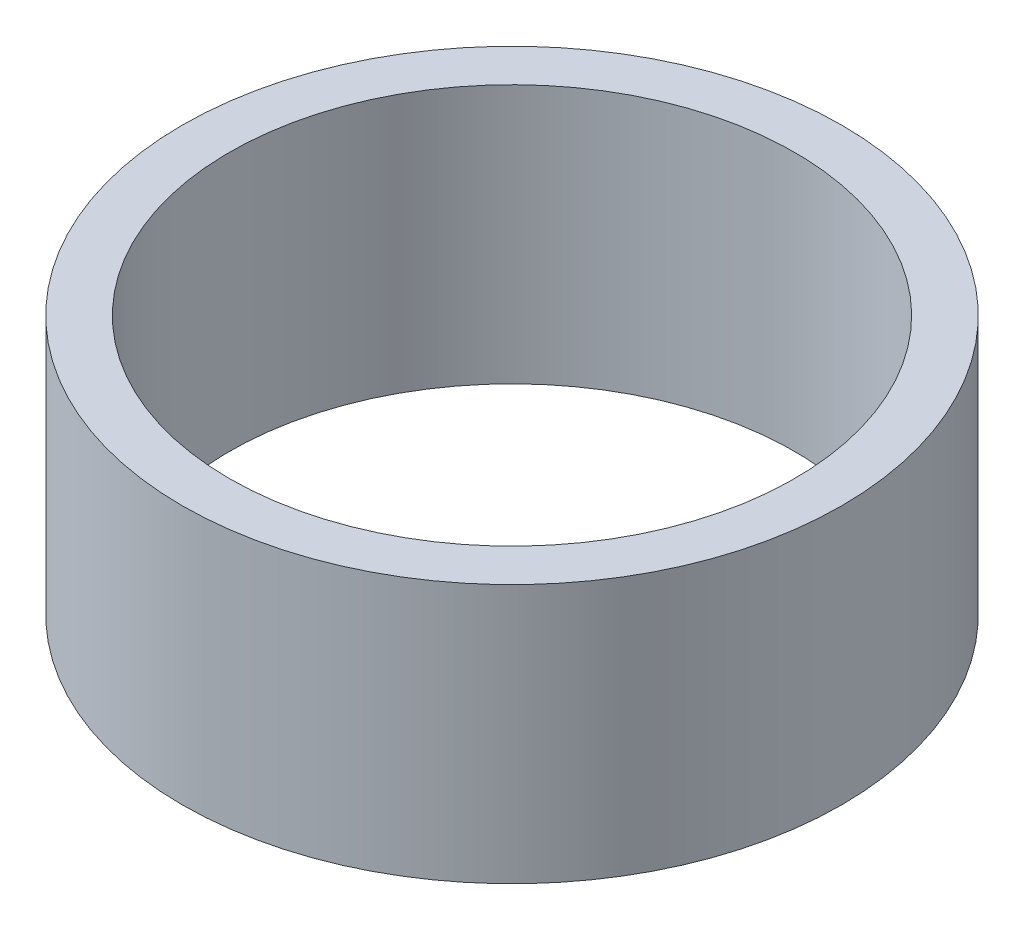
SolidWorks part; units mm, degrees
ref_plane "Front Plane" through (0, 0, 0) normal (0, 0, 1) x (1, 0, 0)
ref_plane "Top Plane" through (0, 0, 0) normal (0, 1, 0) x (1, 0, 0)
ref_plane "Right Plane" through (0, 0, 0) normal (1, 0, 0) x (0, 0, -1)
sketch "Sketch1" plane through (0, 0, 0) normal (0, 1, 0) x (1, 0, 0)
  circle A0 centre (0, 0) radius 28
  circle A1 centre (0, 0) radius 24
  dimension "D1" = 56
  dimension "D2" = 4
extrude "Boss-Extrude1" add sketch "Sketch1" along normal blind 22
